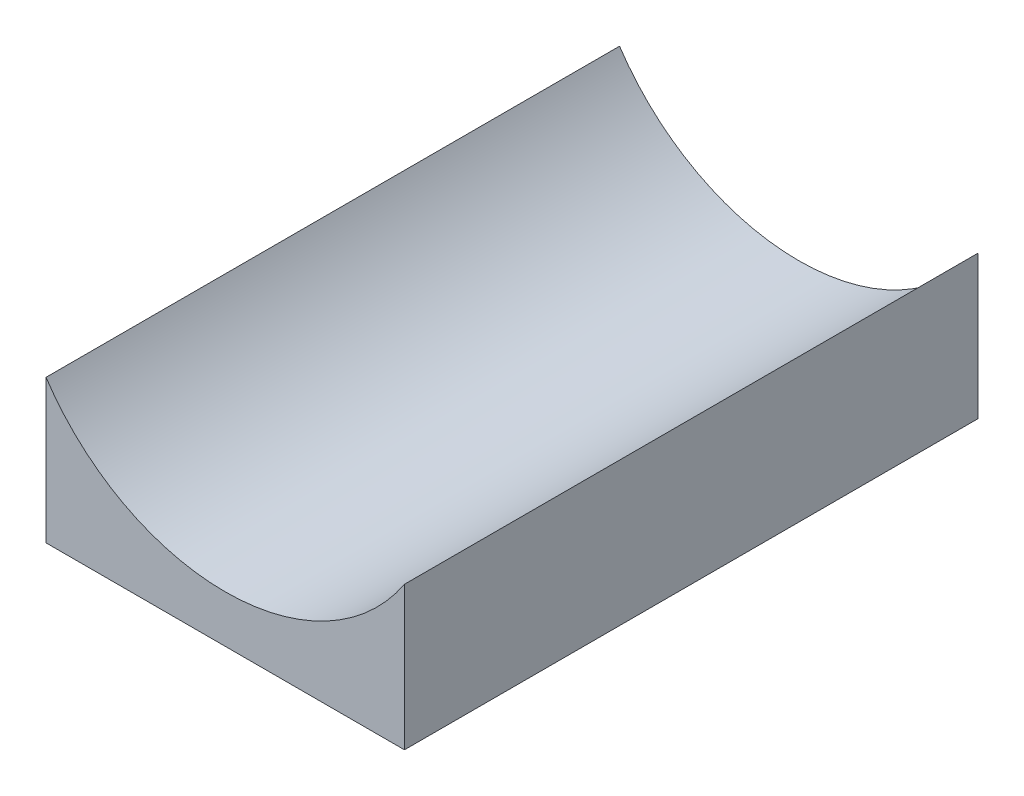
SolidWorks part; units mm, degrees
ref_plane "Front Plane" through (0, 0, 0) normal (0, 0, 1) x (1, 0, 0)
ref_plane "Top Plane" through (0, 0, 0) normal (0, 1, 0) x (1, 0, 0)
ref_plane "Right Plane" through (0, 0, 0) normal (1, 0, 0) x (0, 0, -1)
sketch "Sketch1" plane through (0, 0, 0) normal (0, 0, 1) x (1, 0, 0)
  line L2 (-12.5, 5) -> (-12.5, -5)
  line L3 (-12.5, -5) -> (12.5, -5)
  line L4 (12.5, 5) -> (12.5, -5)
  line L5 (-12.5, 5) -> (12.5, -5) construction
  line L6 (-12.5, -5) -> (12.5, 5) construction
  arc A0 (-12.5, 5) -> (12.5, 5) centre (0, 13.2916) ccw
  point P0 (0, 0)
  point P8 (0, 0)
  dimension "D2" = 30
  dimension "D1" = 25
  dimension "D3" = 10
extrude "Boss-Extrude1" add sketch "Sketch1" along normal blind 40
